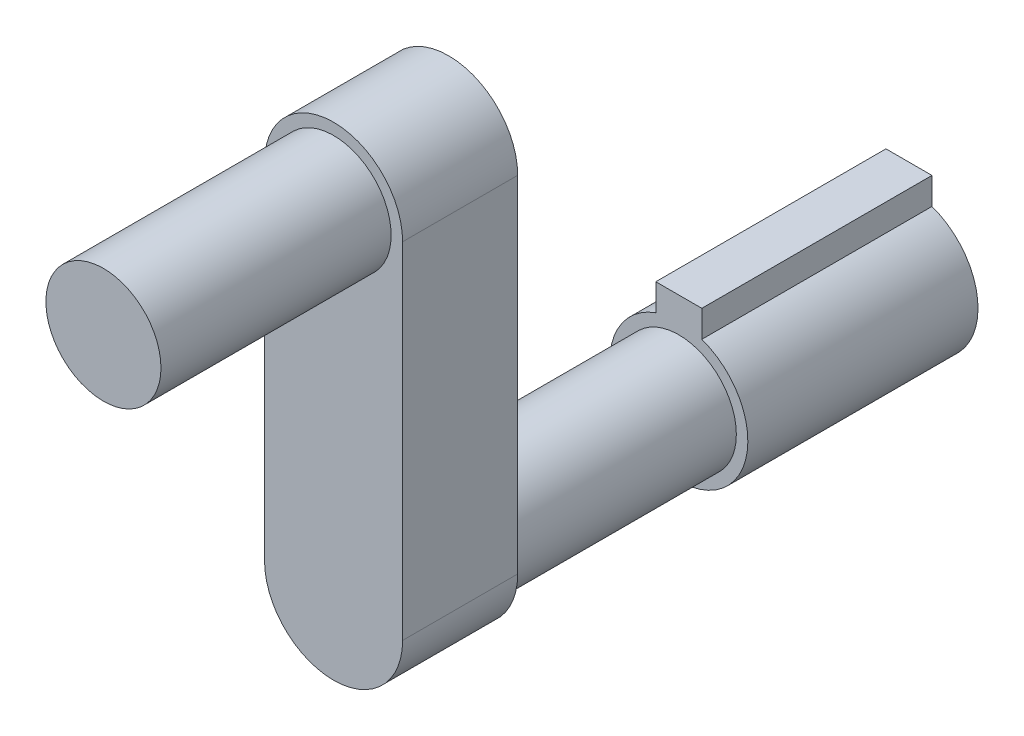
SolidWorks part; units mm, degrees
ref_plane "Front Plane" through (0, 0, 0) normal (0, 0, 1) x (1, 0, 0)
ref_plane "Top Plane" through (0, 0, 0) normal (0, 1, 0) x (1, 0, 0)
ref_plane "Right Plane" through (0, 0, 0) normal (1, 0, 0) x (0, 0, -1)
sketch "Sketch1" plane through (0, 0, 0) normal (0, 0, 1) x (1, 0, 0)
  line L1 (1, 2.0032) -> (-1, 2.0032)
  line L2 (1, 2.0032) -> (1, 3.9968)
  line L3 (1, 3.9968) -> (-1, 3.9968)
  line L4 (-1, 2.0032) -> (-1, 3.9968)
  line L5 (1, 2.0032) -> (-1, 3.9968) construction
  line L6 (1, 3.9968) -> (-1, 2.0032) construction
  circle A0 centre (0, 0) radius 3
  point P3 (0, 3)
  dimension "D2" = 6
  dimension "D1" = 2
  dimension "D3" = 4.12
extrude "Boss-Extrude1" add sketch "Sketch1" along normal blind 10 contours A0 L2 L3 L4
sketch "Sketch2" plane through (0, 0, 10) normal (0, 0, 1) x (1, 0, 0)
  circle A0 centre (0, 0) radius 2.5
  dimension "D1" = 5
extrude "Boss-Extrude2" add sketch "Sketch2" along normal blind 10
sketch "Sketch3" plane through (0, 0, 20) normal (0, 0, 1) x (1, 0, 0)
  line L0 (0, 0) -> (0, 15) construction
  line L1 (-3, 0) -> (-3, 15)
  line L2 (3, 0) -> (3, 15)
  arc A0 (-3, 0) -> (3, 0) centre (0, 0) ccw
  arc A1 (3, 15) -> (-3, 15) centre (0, 15) ccw
  point P3 (0, 7.5)
  dimension "D1" = 3
  dimension "D2" = 15
extrude "Boss-Extrude3" add sketch "Sketch3" along normal blind 5
sketch "Sketch4" plane through (0, 0, 25) normal (0, 0, 1) x (1, 0, 0)
  circle A0 centre (0, 15) radius 2.5
  dimension "D1" = 5
extrude "Boss-Extrude4" add sketch "Sketch4" along normal blind 10
